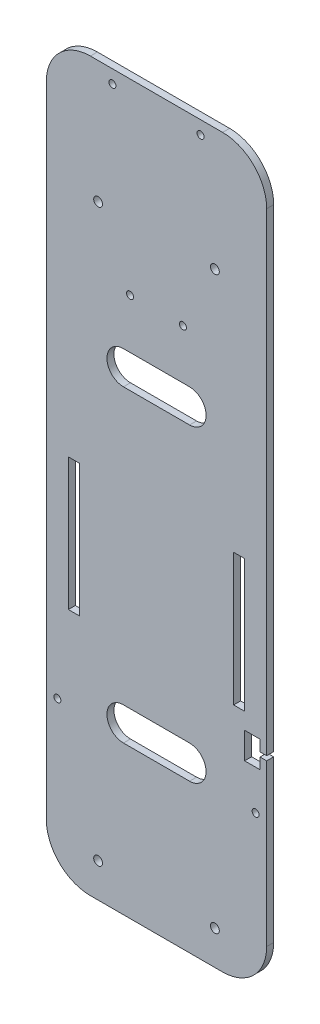
SolidWorks part; units mm, degrees
ref_plane "Front Plane" through (0, 0, 0) normal (0, 0, 1) x (1, 0, 0)
ref_plane "Top Plane" through (0, 0, 0) normal (0, 1, 0) x (1, 0, 0)
ref_plane "Right Plane" through (0, 0, 0) normal (1, 0, 0) x (0, 0, -1)
sketch "Sketch1" plane through (0, 0, 0) normal (0, 0, 1) x (1, 0, 0)
  line L0 (0, 145) -> (0, -145) construction
  line L1 (-50, -145) -> (50, -145)
  line L2 (-50, -145) -> (-50, 145)
  line L3 (-50, 145) -> (50, 145)
  line L4 (50, -145) -> (50, -52)
  line L5 (-50, -145) -> (50, 145) construction
  line L6 (-50, 145) -> (50, -145) construction
  line L7 (-50, 0) -> (50, 0) construction
  line L8 (0, 185) -> (0, 145) construction
  line L9 (-50, 145) -> (50, 145)
  line L10 (-50, 145) -> (-50, 185)
  line L11 (-50, 185) -> (50, 185)
  line L12 (50, 145) -> (50, 185)
  line L13 (-20, 179) -> (20, 179) construction
  line L14 (-15, 70) -> (15, 70) construction
  line L15 (-15, 77.5) -> (15, 77.5)
  line L16 (-15, 62.5) -> (15, 62.5)
  line L17 (47, -50) -> (50, -50)
  line L18 (40, -45) -> (47, -45)
  line L19 (40, -45) -> (40, -57)
  line L20 (40, -57) -> (47, -57)
  line L21 (47, -45) -> (47, -50)
  line L22 (47, -52) -> (50, -52)
  line L23 (47, -52) -> (47, -57)
  line L24 (50, -50) -> (50, 145)
  line L25 (40, -37.5317) -> (35, -37.5317)
  line L26 (-40, 22.4683) -> (-35, 22.4683)
  line L27 (-40, 22.4683) -> (-40, -37.5317)
  line L28 (-40, -37.5317) -> (-35, -37.5317)
  line L29 (-35, 22.4683) -> (-35, -37.5317)
  line L30 (40, 22.4683) -> (40, -37.5317)
  line L31 (40, 22.4683) -> (35, 22.4683)
  line L32 (35, 22.4683) -> (35, -37.5317)
  line L33 (-15, -70) -> (15, -70) construction
  line L34 (-15, -77.5) -> (15, -77.5)
  line L35 (-15, -62.5) -> (15, -62.5)
  circle A0 centre (26.5, 129.5) radius 2
  circle A1 centre (-26.5, 129.5) radius 2
  circle A2 centre (26.5, -129.5) radius 2
  circle A3 centre (-26.5, -129.5) radius 2
  circle A4 centre (-20, 179) radius 1.5875
  circle A5 centre (20, 179) radius 1.5875
  arc A6 (-15, 77.5) -> (-15, 62.5) centre (-15, 70) ccw
  arc A7 (15, 62.5) -> (15, 77.5) centre (15, 70) ccw
  circle A8 centre (-45, -75) radius 1.5875
  circle A9 centre (45, -75) radius 1.5875
  circle A10 centre (-12, 100) radius 1.5875
  circle A11 centre (12, 100) radius 1.5875
  arc A12 (-15, -77.5) -> (-15, -62.5) centre (-15, -70) cw
  arc A13 (15, -62.5) -> (15, -77.5) centre (15, -70) cw
  point P0 (0, 0)
  point P26 (0, 70)
  point P35 (0, 62.5)
  point P59 (0, -70)
  dimension "D3" = 4
  dimension "D7" = 3.175
  dimension "D13" = 3.175
  dimension "D16" = 3.175
  dimension "D1" = 26.5
  dimension "D2" = 129.5
  dimension "D4" = 145
  dimension "D5" = 50
  dimension "D6" = 40
  dimension "D8" = 20
  dimension "D9" = 6
  dimension "D10" = 15
  dimension "D11" = 70
  dimension "D12" = 30
  dimension "D14" = 45
  dimension "D15" = 70
  dimension "D17" = 45
  dimension "D18" = 12
  dimension "D19" = 7
  dimension "D20" = 12
  dimension "D21" = 45
  dimension "D22" = 5
  dimension "D23" = 2
  dimension "D24" = 10
  dimension "D25" = 60
  dimension "D26" = 5
  dimension "D27" = 35
extrude "Boss-Extrude1" add sketch "Sketch1" along normal mid plane 3.175 contours A3 | L3 L12 L11 L10 A4 A5 | A8 | A9 | A10 | A11 | L16 A7 L15 A6 | L29 L26 L27 L28 | A13 L35 A12 L34 | L31 L32 L25 L30 L19 | A1 | A0 | A2
fillet "Fillet1" radius 20 4 edges at (50, -145, 0) (-50, -145, 0) (-50, 185, 0) (50, 185, 0)
